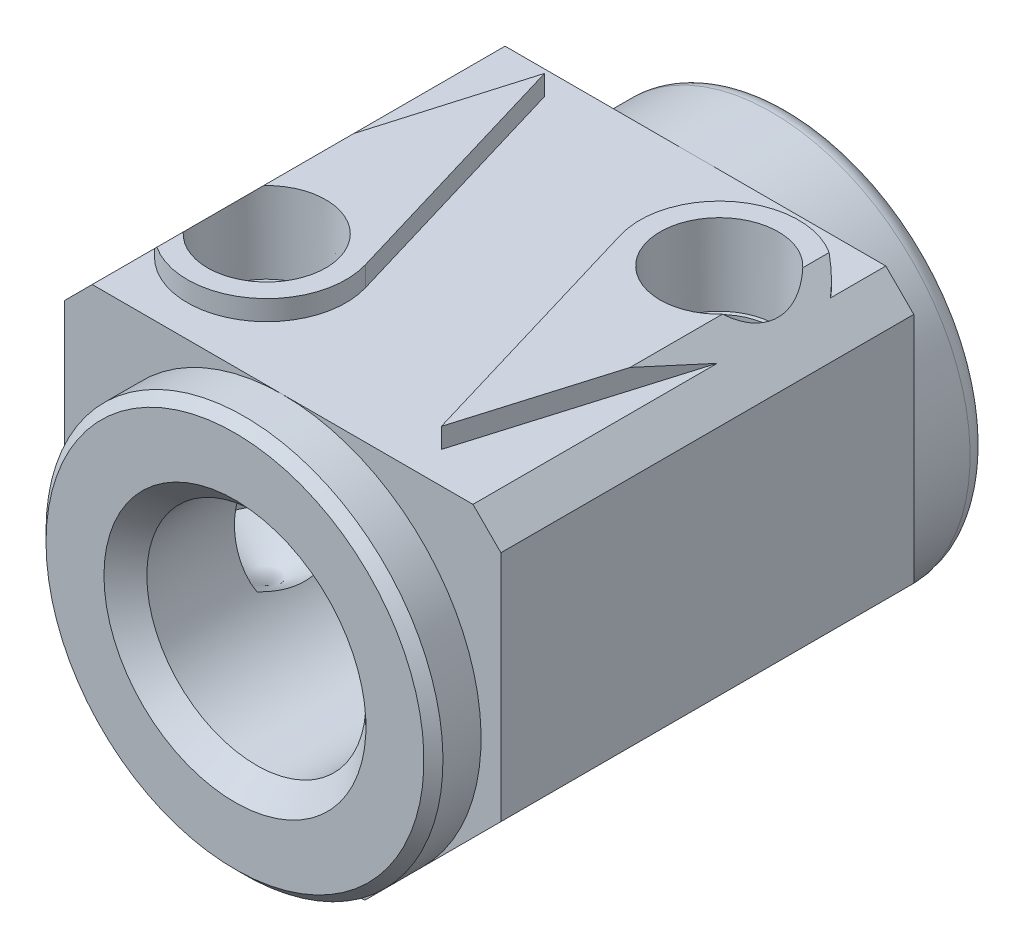
SolidWorks part; units mm, degrees
ref_plane "Front Plane" through (0, 0, 0) normal (0, 0, 1) x (1, 0, 0)
ref_plane "Top Plane" through (0, 0, 0) normal (0, 1, 0) x (1, 0, 0)
ref_plane "Right Plane" through (0, 0, 0) normal (1, 0, 0) x (0, 0, -1)
sketch "Sketch1" plane through (0, 0, 0) normal (0, 0, 1) x (1, 0, 0)
  line L1 (0, 0) -> (34.925, 0)
  line L2 (0, 0) -> (0, 33.3502)
  line L3 (0, 33.3502) -> (34.925, 33.3502)
  line L4 (34.925, 0) -> (34.925, 33.3502)
  dimension "D1" = 33.3502
  dimension "D2" = 34.925
extrude "Extrude1" add sketch "Sketch1" along normal blind 44.45
sketch "Sketch2" plane through (0, 0, 44.45) normal (0, 0, 1) x (1, 0, 0)
  line L0 (0, 15.875) -> (36.8811, 15.875) construction
  line L1 (0, 33.3502) -> (0, 0) construction
  line L2 (24.0381, 0) -> (34.925, 10.8869)
  line L3 (0, 0) -> (34.925, 0) construction
  line L4 (34.925, 0) -> (34.925, 33.3502) construction
  line L5 (10.8869, 0) -> (0, 10.8869)
  line L6 (34.925, 10.8869) -> (38.9532, 7.6762)
  line L7 (38.9532, 7.6762) -> (37.6508, -4.8748)
  line L8 (37.6508, -4.8748) -> (-1.6601, -5.9997)
  line L9 (-1.6601, -5.9997) -> (-2.785, 8.3275)
  line L10 (-2.785, 8.3275) -> (0, 10.8869)
  line L11 (24.0381, 0) -> (18.5282, -3.6908)
  line L12 (18.5282, -3.6908) -> (10.8869, 0)
  circle A0 centre (17.4625, 15.875) radius 15.875 construction
  dimension "D4" = 31.75
  dimension "D1" = 15.875
  dimension "D2" = 45
  dimension "D3" = 45
extrude "Cut-Extrude1" cut sketch "Sketch2" against normal blind 44.45
sketch "Sketch3" plane through (0, 0, 44.45) normal (0, 0, 1) x (1, 0, 0)
  line L0 (34.925, 10.8869) -> (24.0381, 0) construction
  line L1 (10.8869, 0) -> (0, 10.8869) construction
  circle A0 centre (17.4625, 15.875) radius 15.875
  dimension "D1" = 31.75
extrude "Cut-Extrude2" cut sketch "Sketch3" against normal blind 3.81 flip side to cut
hole_wizard "1/8 NPT Tapped Hole1" positions "3DSketch1" profile "Sketch4" size "1/8" standard "Ansi Inch"
sketch3d "3DSketch1"
  line L4 (34.925, 33.3502, 0) -> (0, 33.3502, 0) construction
  line L5 (17.4625, 33.3502, 0) -> (17.4625, 33.3502, 48.4223) construction
  point P0 (7.3025, 33.3502, 31.75)
  point P2 (27.6225, 33.3502, 15.875)
  dimension "D1" = 15.875
  dimension "D2" = 31.75
  dimension "D3" = 10.16
  dimension "D4" = 10.16
sketch "Sketch4" plane through (7.3025, 33.3502, 31.75) normal (1, 0, 0) x (0, 0, 1)
  line L0 (0, 0) -> (0, 24.3775)
  line L1 (4.2164, 21.844) -> (0, 24.3775)
  line L2 (-4.2164, 21.844) -> (0, 24.3775) construction
  line L3 (4.2164, 21.844) -> (4.2164, 6.35)
  line L4 (4.2164, 6.35) -> (4.5374, 6.35)
  line L5 (4.5374, 6.35) -> (4.7275, 0)
  line L6 (-4.5374, 6.35) -> (-4.7275, 0) construction
  line L7 (4.7275, 0) -> (0, 0)
  line L8 (0, -6.35) -> (0, 107.95) construction
  line L11 (-4.2164, 6.35) -> (-4.5374, 6.35) construction
  dimension "Tap Drill Dia." = 8.4328
  dimension "Tap Drill Depth" = 21.844
  dimension "Thread Dia." = 9.4551
  dimension "Thread Angle" = 3.43
  dimension "Thread Depth" = 6.35
  dimension "Drill Angle" = 118
cosmetic thread "Hole Thread1" parameters "D1"=6.35
cosmetic thread "Hole Thread2" parameters "D1"=6.35
sketch "Sketch5" plane through (0, 0, 0) normal (0, 0, -1) x (-1, 0, 0)
  line L0 (-34.925, 10.8869) -> (-24.0381, 0) construction
  line L1 (-10.8869, 0) -> (0, 10.8869) construction
  circle A0 centre (-17.4625, 15.875) radius 15.875
  dimension "D1" = 31.75
extrude "Cut-Extrude3" cut sketch "Sketch5" against normal blind 7.62 flip side to cut
sketch "Sketch6" plane through (0, 33.3502, 0) normal (0, 1, 0) x (-1, 0, 0)
  line L3 (-13.3878, 29.9357) -> (-7.3025, 9.525)
  line L5 (-7.3025, 9.525) -> (-0.9985, 30.9871)
  line L6 (-27.6225, 38.1) -> (-33.7078, 17.6893)
  line L7 (-27.6225, 38.1) -> (-21.5372, 17.6893)
  arc A0 (-1.5873, 28.9826) -> (-13.3878, 29.9357) centre (-7.3025, 31.75) ccw
  arc A1 (-33.7078, 17.6893) -> (-21.5372, 17.6893) centre (-27.6225, 15.875) ccw
  line M3 (-34.925, 7.62) -> (0, 7.62)
  line M4 (0, 7.62) -> (0, 40.64)
  line M5 (0, 40.64) -> (-34.925, 40.64)
  line M6 (-34.925, 40.64) -> (-34.925, 7.62)
  dimension "D1" = 12.7
  dimension "D2" = 12.7
extrude "Cut-Extrude4" cut sketch "Sketch6" against normal blind 1.6002 contours A1 L6 L7 A0 L5 L3 M3 M4 M5 M6
sketch "Sketch8" plane through (0, 0, 44.45) normal (0, 0, 1) x (1, 0, 0)
  line L0 (0, 29.5148) -> (8.828, 38.3428)
  line L1 (0, 31.75) -> (0, 10.8869) construction
  line L2 (34.925, 29.5148) -> (29.9885, 34.4513)
  line L3 (34.925, 10.8869) -> (34.925, 31.75) construction
  line L4 (29.9885, 34.4513) -> (8.828, 38.3428)
  line L5 (8.828, 38.3428) -> (11.0224, 37.7384)
  line L6 (0, 29.5148) -> (-4.6203, 29.437)
  line L7 (-4.6203, 29.437) -> (-2.7258, 41.4552)
  line L8 (-2.7258, 41.4552) -> (37.7692, 38.0948)
  line L9 (37.7692, 38.0948) -> (34.925, 29.5148)
  line L10 (0, 31.75) -> (2.2352, 31.75)
  line L11 (17.4625, 31.75) -> (0, 31.75) construction
  line L12 (34.925, 31.75) -> (32.6898, 31.75)
  line L13 (27.6225, 31.75) -> (33.7078, 31.75) construction
  dimension "D1" = 2.2352
  dimension "D2" = 45
  dimension "D4" = 45
  dimension "D5" = 2.2352
extrude "Cut-Extrude5" cut sketch "Sketch8" against normal through all
hole_wizard "5/8 (0.625) Diameter Hole1" positions "3DSketch4" profile "Sketch11" hole size "5/8" standard "Ansi Inch" end condition through all
sketch3d "3DSketch4"
  circle A0 centre (17.4625, 15.875, 44.45) radius 15.875 construction
  point P0 (17.4625, 15.875, 44.45)
  point P5 (17.4625, 15.875, 60.325)
sketch "Sketch11" plane through (17.4625, 15.875, 44.45) normal (1, 0, 0) x (0, -1, 0)
  line L0 (0, 0) -> (0, 44.45)
  line L1 (0, 44.45) -> (7.9375, 44.45)
  line L2 (7.9375, 44.45) -> (7.9375, 0)
  line L5 (7.9375, 0) -> (0, 0)
  line L11 (0, -6.35) -> (0, 107.95) construction
  dimension "Thru Hole Dia." = 15.875
  dimension "Thru Hole Depth" = 44.45
hole_wizard "3/4-16 Tapped Hole1" positions "3DSketch5" profile "Sketch12" tap size "3/4-16" standard "Ansi Inch"
sketch3d "3DSketch5"
  circle A0 centre (17.4625, 15.875, 44.45) radius 7.9375 construction
  point P0 (17.4625, 15.875, 44.45)
  point P3 (21.5284, 22.6921, 44.45)
  point P7 (17.4625, 15.875, 52.3875)
  point P8 (17.4625, 15.875, 44.45)
sketch "Sketch12" plane through (17.4625, 15.875, 44.45) normal (1, 0, 0) x (0, -1, 0)
  line L0 (0, 0) -> (0, 30.6653)
  line L1 (0, 30.6653) -> (8.763, 25.4)
  line L2 (8.763, 25.4) -> (8.763, 0)
  line L5 (8.763, 0) -> (0, 0)
  line L10 (0, 30.6653) -> (-8.763, 25.4) construction
  line L11 (0, -6.35) -> (0, 107.95) construction
  dimension "Tap Drill Dia." = 17.526
  dimension "Tap Drill Depth" = 25.4
  dimension "Drill Angle" = 118
cosmetic thread "Hole Thread3" parameters "D1"=9.652, "D2"=19.05
ref_plane "Plane1" through (0, 0, 0) normal (0, 0, -1) x (-1, 0, 0)
ref_plane "Plane2" through (0, 0, 5.715) normal (0, 0, -1) x (-1, 0, 0)
sketch "Sketch16" plane through (0, 0, 5.715) normal (0, 0, -1) x (-1, 0, 0)
  circle A0 centre (-17.4625, 15.875) radius 10.16
  circle A1 centre (-17.4625, 15.875) radius 7.9375 construction
  dimension "D1" = 20.32
extrude "Cut-Extrude7" cut sketch "Sketch16" against normal blind 3.556
chamfer "Chamfer1" distance 0.762 angle 45 2 edges at (25.4, 15.875, 0) (33.3375, 15.875, 44.45)
fillet "Fillet1" radius 1.524 1 edges at (1.5875, 15.875, 0)
chamfer "Chamfer2" distance 1.7145 angle 45 1 edges at (26.2255, 15.875, 44.45)
sketch "Sketch17" plane through (0, 0, 0) normal (0, 0, -1) x (-1, 0, 0)
  circle A0 centre (-17.4625, 15.875) radius 8.763
  dimension "D1" = 17.526
ref_plane "Plane3" through (0, 0, 12.446) normal (0, 0, -1) x (-1, 0, 0)
sketch "Sketch18" plane through (0, 0, 12.446) normal (0, 0, -1) x (-1, 0, 0)
  circle A0 centre (-17.4625, 15.875) radius 8.763
  dimension "D1" = 17.526
extrude "Cut-Extrude9" cut sketch "Sketch18" against normal blind 7.62
